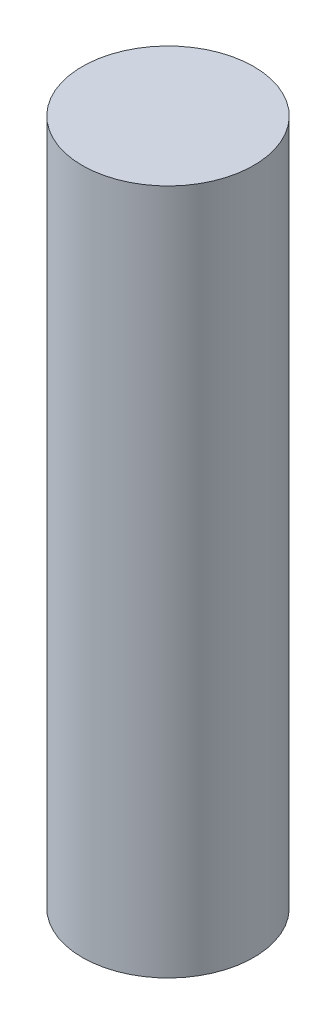
SolidWorks part; units mm, degrees
ref_plane "Front Plane" through (0, 0, 0) normal (0, 0, 1) x (1, 0, 0)
ref_plane "Top Plane" through (0, 0, 0) normal (0, 1, 0) x (1, 0, 0)
ref_plane "Right Plane" through (0, 0, 0) normal (1, 0, 0) x (0, 0, -1)
sketch "Sketch1" plane through (0, 0, 0) normal (0, 1, 0) x (1, 0, 0)
  circle A0 centre (0, 0) radius 0.25
  dimension "D1" = 0.5
extrude "Boss-Extrude1" add sketch "Sketch1" along normal blind 2
